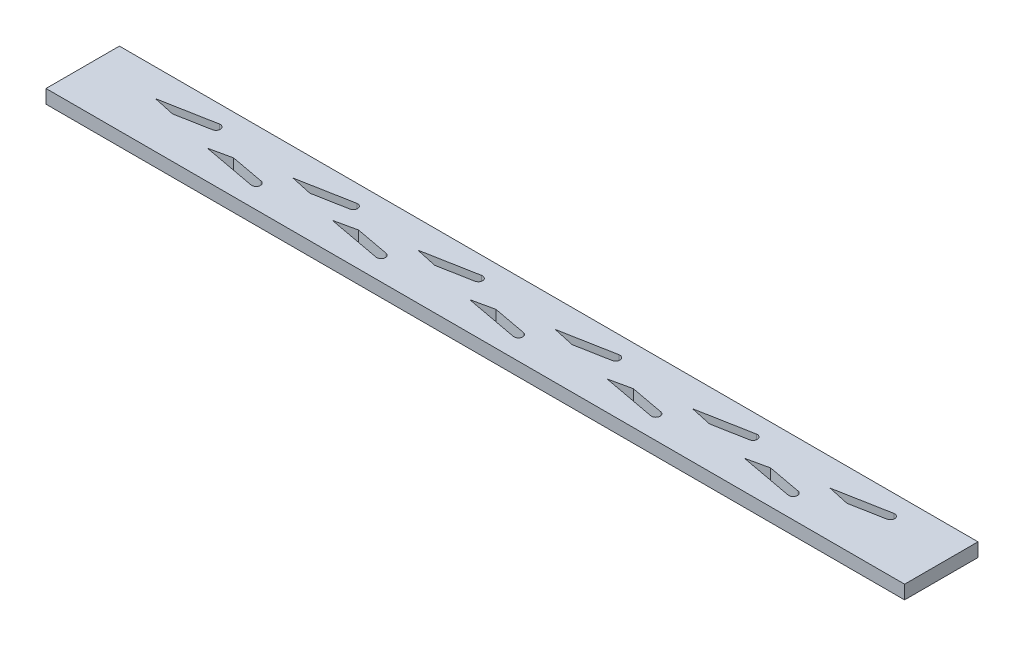
SolidWorks part; units mm, degrees
ref_plane "Front Plane" through (0, 0, 0) normal (0, 0, 1) x (1, 0, 0)
ref_plane "Top Plane" through (0, 0, 0) normal (0, 1, 0) x (1, 0, 0)
ref_plane "Right Plane" through (0, 0, 0) normal (1, 0, 0) x (0, 0, -1)
sketch "Sketch4" plane through (0, 0, 0) normal (0, 1, 0) x (1, 0, 0)
  line L1 (0, 0) -> (200, 0)
  line L2 (0, 0) -> (0, 17.1)
  line L3 (0, 17.1) -> (200, 17.1)
  line L4 (200, 0) -> (200, 17.1)
  dimension "D1" = 17.1
  dimension "D2" = 200
extrude "Boss-Extrude2" add sketch "Sketch4" along normal blind 3.175
sketch "Sketch5" plane through (0, 3.175, 0) normal (0, 1, 0) x (1, 0, 0)
  line L0 (0, 0) -> (200, 0) construction
  line L2 (0, 0) -> (200, 0)
  line L3 (0, 0) -> (0, 17.1)
  line L4 (0, 17.1) -> (200, 17.1)
  line L5 (200, 0) -> (200, 17.1)
  line L6 (11.5393, 2.25) -> (11.5393, 15.2) construction
  line L7 (72.6396, 14.9684) -> (72.6396, 2.0184) construction
  line L8 (88.6396, 14.9684) -> (88.6396, 2.0184) construction
  line L9 (30.8216, 6.75) -> (35.8574, 7.847)
  line L10 (35.8574, 7.847) -> (43.7223, 6.3831)
  line L11 (30.8216, 6.75) -> (43.3564, 4.4169)
  line L12 (46.8216, 10.7) -> (51.8574, 9.603)
  line L13 (46.8216, 10.7) -> (59.3564, 13.0331)
  line L14 (51.8574, 9.603) -> (59.7223, 11.0669)
  line L15 (104.6396, 14.9684) -> (104.6396, 2.0184) construction
  line L16 (120.6396, 14.9684) -> (120.6396, 2.0184) construction
  line L17 (136.6396, 14.9684) -> (136.6396, 2.0184) construction
  line L18 (152.6396, 14.9684) -> (152.6396, 2.0184) construction
  line L19 (168.6396, 14.9684) -> (168.6396, 2.0184) construction
  line L20 (184.6396, 14.9684) -> (184.6396, 2.0184) construction
  line L21 (14.8216, 10.7) -> (19.8574, 9.603)
  line L22 (19.8574, 9.603) -> (27.7223, 11.0669)
  line L23 (14.8216, 10.7) -> (27.3564, 13.0331)
  line L24 (75.9218, 10.7) -> (80.9576, 9.603)
  line L25 (80.9576, 9.603) -> (88.8225, 11.0669)
  line L26 (75.9218, 10.7) -> (88.4566, 13.0331)
  line L27 (107.9218, 10.7) -> (112.9576, 9.603)
  line L28 (112.9576, 9.603) -> (120.8225, 11.0669)
  line L29 (107.9218, 10.7) -> (120.4566, 13.0331)
  line L30 (139.9218, 10.7) -> (144.9576, 9.603)
  line L31 (144.9576, 9.603) -> (152.8225, 11.0669)
  line L32 (139.9218, 10.7) -> (152.4566, 13.0331)
  line L33 (171.9218, 10.7) -> (176.9576, 9.603)
  line L34 (176.9576, 9.603) -> (184.8225, 11.0669)
  line L35 (171.9218, 10.7) -> (184.4566, 13.0331)
  line L36 (59.9218, 6.75) -> (72.4566, 4.4169)
  line L37 (64.9576, 7.847) -> (72.8225, 6.3831)
  line L38 (59.9218, 6.75) -> (64.9576, 7.847)
  line L39 (91.9218, 6.75) -> (104.4566, 4.4169)
  line L40 (96.9576, 7.847) -> (104.8225, 6.3831)
  line L41 (91.9218, 6.75) -> (96.9576, 7.847)
  line L42 (59.5393, 15.2) -> (59.5393, 2.25) construction
  line L43 (0, 8.55) -> (200, 8.55) construction
  line L44 (0, 2.25) -> (200, 2.25) construction
  line L45 (200, 15.2) -> (0, 15.2) construction
  line L46 (43.5393, 2.25) -> (43.5393, 15.2) construction
  line L47 (0, 5.4) -> (200, 5.4) construction
  line L48 (0, 12.05) -> (200, 12.05) construction
  line L49 (27.5393, 15.2) -> (27.5393, 2.25) construction
  line L50 (123.9218, 6.75) -> (136.4566, 4.4169)
  line L51 (128.9576, 7.847) -> (136.8225, 6.3831)
  line L52 (123.9218, 6.75) -> (128.9576, 7.847)
  line L53 (155.9218, 6.75) -> (168.4566, 4.4169)
  line L54 (160.9576, 7.847) -> (168.8225, 6.3831)
  line L55 (155.9218, 6.75) -> (160.9576, 7.847)
  circle A0 centre (88.6396, 12.05) radius 3.15 construction
  arc A1 (43.7223, 6.3831) -> (43.3564, 4.4169) centre (43.5393, 5.4) cw
  arc A2 (59.3564, 13.0331) -> (59.7223, 11.0669) centre (59.5393, 12.05) cw
  circle A3 centre (120.6396, 12.05) radius 3.15 construction
  circle A4 centre (152.6396, 12.05) radius 3.15 construction
  circle A5 centre (184.6396, 12.05) radius 3.15 construction
  circle A6 centre (72.6396, 5.4) radius 3.15 construction
  circle A7 centre (104.6396, 5.4) radius 3.15 construction
  circle A8 centre (136.6396, 5.4) radius 3.15 construction
  circle A9 centre (168.6396, 5.4) radius 3.15 construction
  circle A10 centre (27.5393, 12.05) radius 3.15 construction
  arc A11 (27.3564, 13.0331) -> (27.7223, 11.0669) centre (27.5393, 12.05) cw
  arc A12 (88.4566, 13.0331) -> (88.8225, 11.0669) centre (88.6396, 12.05) cw
  arc A13 (120.4566, 13.0331) -> (120.8225, 11.0669) centre (120.6396, 12.05) cw
  arc A14 (152.4566, 13.0331) -> (152.8225, 11.0669) centre (152.6396, 12.05) cw
  circle A15 centre (43.5393, 5.4) radius 3.15 construction
  circle A16 centre (59.5393, 12.05) radius 3.15 construction
  arc A17 (184.4566, 13.0331) -> (184.8225, 11.0669) centre (184.6396, 12.05) cw
  arc A18 (72.8225, 6.3831) -> (72.4566, 4.4169) centre (72.6396, 5.4) cw
  arc A19 (104.8225, 6.3831) -> (104.4566, 4.4169) centre (104.6396, 5.4) cw
  arc A20 (136.8225, 6.3831) -> (136.4566, 4.4169) centre (136.6396, 5.4) cw
  arc A21 (168.8225, 6.3831) -> (168.4566, 4.4169) centre (168.6396, 5.4) cw
  dimension "D22" = 6.3
  dimension "D1" = 200
  dimension "D2" = 200
  dimension "D3" = 1.35
  dimension "D4" = 5.1539
  dimension "D5" = 2.25
  dimension "D6" = 3.15
  dimension "D7" = 16
  dimension "D8" = 16
  dimension "D9" = 3.15
  dimension "D10" = 3.5
  dimension "D11" = 4.5
  dimension "D12" = 4.5
  dimension "D13" = 27.5393
  dimension "D14" = 5.1539
  dimension "D15" = 12.75
  dimension "D16" = 8
  dimension "D17" = 2
  dimension "D18" = 2
  dimension "D19" = 8
  dimension "D20" = 12.75
  dimension "D21" = 3.15
  dimension "D23" = 16
extrude "Cut-Extrude3" cut sketch "Sketch5" against normal blind 3.175 contours A2 L13 L12 L14 | A18 L37 L38 L36 | A12 L26 L24 L25 | A19 L40 L41 L39 | A13 L29 L27 L28 | A14 L32 L30 L31 | A17 L35 L33 L34 | L21 L22 A11 L23 | L10 A1 L11 L9 | L51 A20 L50 L52 | L53 A21 L54 L55
sketch "Sketch2" plane through (0, 0, 0) normal (0, 1, 0) x (1, 0, 0)
  line L0 (240.7868, 258.8081) -> (423.9116, 240.5299) construction
  line L1 (58.3044, 14.9478) -> (28.1971, 8.9694)
  line L2 (44.1199, 8.496) -> (71.4399, 2.4874)
  line L3 (59.5393, 8.9) -> (89.2652, 15.1372)
  line L4 (35.8574, 7.847) -> (30.8216, 6.75)
  line L5 (43.7223, 6.3831) -> (35.8574, 7.847)
  line L6 (30.8216, 6.75) -> (43.3564, 4.4169)
  line L7 (35.8574, 7.847) -> (30.8216, 6.75) construction
  line L8 (43.7223, 6.3831) -> (35.8574, 7.847) construction
  line L9 (30.8216, 6.75) -> (43.3564, 4.4169) construction
  line L10 (46.8216, 10.7) -> (51.8574, 9.603)
  line L11 (0, 0) -> (200, 0)
  line L12 (200, 0) -> (200, 17.1)
  line L13 (200, 17.1) -> (0, 17.1)
  line L14 (0, 17.1) -> (0, 0)
  line L15 (0, 0) -> (200, 0) construction
  line L16 (200, 0) -> (200, 17.1) construction
  line L17 (200, 17.1) -> (0, 17.1) construction
  line L18 (0, 17.1) -> (0, 0) construction
  line L19 (51.8574, 9.603) -> (59.7223, 11.0669)
  line L20 (59.3564, 13.0331) -> (46.8216, 10.7)
  line L21 (46.8216, 10.7) -> (51.8574, 9.603) construction
  line L22 (51.8574, 9.603) -> (59.7223, 11.0669) construction
  line L23 (59.3564, 13.0331) -> (46.8216, 10.7) construction
  line L24 (75.9218, 10.7) -> (80.9576, 9.603)
  line L25 (80.9576, 9.603) -> (88.8225, 11.0669)
  line L26 (88.4566, 13.0331) -> (75.9218, 10.7)
  line L27 (75.9218, 10.7) -> (80.9576, 9.603) construction
  line L28 (80.9576, 9.603) -> (88.8225, 11.0669) construction
  line L29 (88.4566, 13.0331) -> (75.9218, 10.7) construction
  line L30 (14.8216, 10.7) -> (19.8574, 9.603)
  line L31 (19.8574, 9.603) -> (27.7223, 11.0669)
  line L32 (27.3564, 13.0331) -> (14.8216, 10.7)
  line L33 (14.8216, 10.7) -> (19.8574, 9.603) construction
  line L34 (19.8574, 9.603) -> (27.7223, 11.0669) construction
  line L35 (27.3564, 13.0331) -> (14.8216, 10.7) construction
  line L36 (139.9218, 10.7) -> (144.9576, 9.603)
  line L37 (144.9576, 9.603) -> (152.8225, 11.0669)
  line L38 (152.4566, 13.0331) -> (139.9218, 10.7)
  line L39 (139.9218, 10.7) -> (144.9576, 9.603) construction
  line L40 (144.9576, 9.603) -> (152.8225, 11.0669) construction
  line L41 (152.4566, 13.0331) -> (139.9218, 10.7) construction
  line L42 (112.9576, 9.603) -> (120.8225, 11.0669)
  line L43 (120.4566, 13.0331) -> (107.9218, 10.7)
  line L44 (107.9218, 10.7) -> (112.9576, 9.603)
  line L45 (112.9576, 9.603) -> (120.8225, 11.0669) construction
  line L46 (120.4566, 13.0331) -> (107.9218, 10.7) construction
  line L47 (107.9218, 10.7) -> (112.9576, 9.603) construction
  line L48 (171.9218, 10.7) -> (176.9576, 9.603)
  line L49 (176.9576, 9.603) -> (184.8225, 11.0669)
  line L50 (184.4566, 13.0331) -> (171.9218, 10.7)
  line L51 (171.9218, 10.7) -> (176.9576, 9.603) construction
  line L52 (176.9576, 9.603) -> (184.8225, 11.0669) construction
  line L53 (184.4566, 13.0331) -> (171.9218, 10.7) construction
  line L54 (123.9218, 6.75) -> (136.4566, 4.4169)
  line L55 (136.8225, 6.3831) -> (128.9576, 7.847)
  line L56 (128.9576, 7.847) -> (123.9218, 6.75)
  line L57 (123.9218, 6.75) -> (136.4566, 4.4169) construction
  line L58 (136.8225, 6.3831) -> (128.9576, 7.847) construction
  line L59 (128.9576, 7.847) -> (123.9218, 6.75) construction
  line L60 (91.9218, 6.75) -> (104.4566, 4.4169)
  line L61 (104.8225, 6.3831) -> (96.9576, 7.847)
  line L62 (96.9576, 7.847) -> (91.9218, 6.75)
  line L63 (91.9218, 6.75) -> (104.4566, 4.4169) construction
  line L64 (104.8225, 6.3831) -> (96.9576, 7.847) construction
  line L65 (96.9576, 7.847) -> (91.9218, 6.75) construction
  line L66 (59.9218, 6.75) -> (72.4566, 4.4169)
  line L67 (72.8225, 6.3831) -> (64.9576, 7.847)
  line L68 (64.9576, 7.847) -> (59.9218, 6.75)
  line L69 (59.9218, 6.75) -> (72.4566, 4.4169) construction
  line L70 (72.8225, 6.3831) -> (64.9576, 7.847) construction
  line L71 (64.9576, 7.847) -> (59.9218, 6.75) construction
  line L72 (168.8225, 6.3831) -> (160.9576, 7.847)
  line L73 (160.9576, 7.847) -> (155.9218, 6.75)
  line L74 (155.9218, 6.75) -> (168.4566, 4.4169)
  line L75 (168.8225, 6.3831) -> (160.9576, 7.847) construction
  line L76 (160.9576, 7.847) -> (155.9218, 6.75) construction
  line L77 (155.9218, 6.75) -> (168.4566, 4.4169) construction
  line L78 (72.7041, 8.5493) -> (103.4387, 2.4879)
  line L79 (88.6139, 8.9001) -> (119.4407, 14.9629)
  line L80 (104.6391, 8.55) -> (136.0254, 2.3105)
  line L81 (120.6396, 8.9) -> (152.0253, 15.1395)
  line L82 (137.2538, 8.4895) -> (168.6396, 2.25)
  line L83 (153.2538, 8.9605) -> (184.3499, 15.1424)
  line L84 (168.6396, 8.55) -> (200, 14.7845)
  line L85 (42.8627, 2.3235) -> (19.2585, 6.75)
  line L87 (0, 11.05) -> (0, 6.05)
  line L88 (7.7734, 6.05) -> (0, 6.05)
  line L89 (7.7734, 11.05) -> (26.9258, 15.1397)
  line L90 (7.7734, 11.05) -> (0, 11.05)
  line L91 (184.9349, 15.2) -> (186.5848, 15.2)
  line L92 (188.8707, 14.1428) -> (190.0693, 12.7326)
  line L93 (191.5088, 11.7973) -> (195.2397, 10.7)
  line L94 (195.2397, 10.7) -> (200, 10.7)
  line L95 (200, 10.7) -> (200, 14.7845)
  circle A0 centre (27.5393, 12.05) radius 3.15 construction
  arc A1 (43.3564, 4.4169) -> (43.7223, 6.3831) centre (43.5393, 5.4) ccw
  arc A2 (43.3564, 4.4169) -> (43.7223, 6.3831) centre (43.5393, 5.4) ccw construction
  arc A3 (59.7223, 11.0669) -> (59.3564, 13.0331) centre (59.5393, 12.05) ccw
  arc A4 (59.7223, 11.0669) -> (59.3564, 13.0331) centre (59.5393, 12.05) ccw construction
  arc A5 (88.8225, 11.0669) -> (88.4566, 13.0331) centre (88.6396, 12.05) ccw
  arc A6 (88.8225, 11.0669) -> (88.4566, 13.0331) centre (88.6396, 12.05) ccw construction
  arc A7 (27.7223, 11.0669) -> (27.3564, 13.0331) centre (27.5393, 12.05) ccw
  arc A8 (27.7223, 11.0669) -> (27.3564, 13.0331) centre (27.5393, 12.05) ccw construction
  arc A9 (152.8225, 11.0669) -> (152.4566, 13.0331) centre (152.6396, 12.05) ccw
  arc A10 (152.8225, 11.0669) -> (152.4566, 13.0331) centre (152.6396, 12.05) ccw construction
  arc A11 (120.8225, 11.0669) -> (120.4566, 13.0331) centre (120.6396, 12.05) ccw
  arc A12 (120.8225, 11.0669) -> (120.4566, 13.0331) centre (120.6396, 12.05) ccw construction
  arc A13 (184.8225, 11.0669) -> (184.4566, 13.0331) centre (184.6396, 12.05) ccw
  arc A14 (184.8225, 11.0669) -> (184.4566, 13.0331) centre (184.6396, 12.05) ccw construction
  arc A15 (136.4566, 4.4169) -> (136.8225, 6.3831) centre (136.6396, 5.4) ccw
  arc A16 (136.4566, 4.4169) -> (136.8225, 6.3831) centre (136.6396, 5.4) ccw construction
  arc A17 (104.4566, 4.4169) -> (104.8225, 6.3831) centre (104.6396, 5.4) ccw
  arc A18 (104.4566, 4.4169) -> (104.8225, 6.3831) centre (104.6396, 5.4) ccw construction
  arc A19 (72.4566, 4.4169) -> (72.8225, 6.3831) centre (72.6396, 5.4) ccw
  arc A20 (72.4566, 4.4169) -> (72.8225, 6.3831) centre (72.6396, 5.4) ccw construction
  arc A21 (168.4566, 4.4169) -> (168.8225, 6.3831) centre (168.6396, 5.4) ccw
  arc A22 (168.4566, 4.4169) -> (168.8225, 6.3831) centre (168.6396, 5.4) ccw construction
  circle A23 centre (43.5393, 5.4) radius 3.15 construction
  circle A24 centre (59.5393, 12.05) radius 3.15 construction
  circle A25 centre (72.6396, 5.4) radius 3.15 construction
  circle A26 centre (88.6396, 12.05) radius 3.15 construction
  circle A27 centre (104.6396, 5.4) radius 3.15 construction
  circle A28 centre (120.6396, 12.05) radius 3.15 construction
  circle A29 centre (136.6396, 5.4) radius 3.15 construction
  circle A30 centre (152.6396, 12.05) radius 3.15 construction
  circle A31 centre (168.6396, 5.4) radius 3.15 construction
  circle A32 centre (184.6396, 12.05) radius 3.15 construction
  arc A33 (168.6396, 2.25) -> (168.6396, 8.55) centre (169.2658, 5.4) ccw
  arc A34 (153.2538, 8.9605) -> (152.0253, 15.1395) centre (152.6396, 12.05) ccw
  arc A35 (137.2538, 8.4895) -> (136.0254, 2.3105) centre (136.6395, 5.4) cw
  arc A36 (119.4407, 14.9629) -> (120.6396, 8.9) centre (120.037, 11.9309) cw
  arc A37 (104.6391, 8.55) -> (103.4387, 2.4879) centre (104.0366, 5.5194) cw
  arc A38 (89.2652, 15.1372) -> (88.6139, 8.9001) centre (87.9809, 12.1188) cw
  arc A39 (71.4399, 2.4874) -> (72.7041, 8.5493) centre (72.105, 5.5115) ccw
  arc A40 (58.3044, 14.9478) -> (59.5393, 8.9) centre (58.9056, 11.9206) cw
  arc A41 (44.1199, 8.496) -> (42.8627, 2.3235) centre (43.4433, 5.4196) cw
  arc A42 (28.1971, 8.9694) -> (26.9258, 15.1397) centre (27.5836, 12.0591) ccw
  arc A44 (190.0693, 12.7326) -> (191.5088, 11.7973) centre (192.3552, 14.6754) ccw
  arc A45 (186.5848, 15.2) -> (188.8707, 14.1428) centre (186.5848, 12.2) cw
  arc A46 (184.3499, 15.1424) -> (184.9349, 15.2) centre (184.9349, 12.2) cw
  point P100 (0, 8.55)
  point P122 (184.6396, 15.2)
  point P123 (0, 8.55)
  dimension "D9" = 0
  dimension "D11" = 0
  dimension "D12" = 0
  dimension "D13" = 6.3
  dimension "D14" = 6.3
  dimension "D15" = 6.3
  dimension "D16" = 6.3
  dimension "D18" = 6.3
  dimension "D21" = 6.3
  dimension "D25" = 3
  dimension "D19" = 6.3
  dimension "D22" = 6.3
  dimension "D17" = 6.3
  dimension "D20" = 6.3
  dimension "D23" = 6.3
  dimension "D24" = 3.15
  dimension "D26" = 3
  dimension "D27" = 3
  dimension "D28" = 3.15
  dimension "D1" = 0
  dimension "D2" = 0
  dimension "D3" = 0
  dimension "D4" = 0
  dimension "D5" = 0
  dimension "D6" = 0
  dimension "D7" = 0
  dimension "D8" = 0
  dimension "D10" = 0
  dimension "D30" = 19.5842
  dimension "D32" = 5
  dimension "D33" = 7.7734
